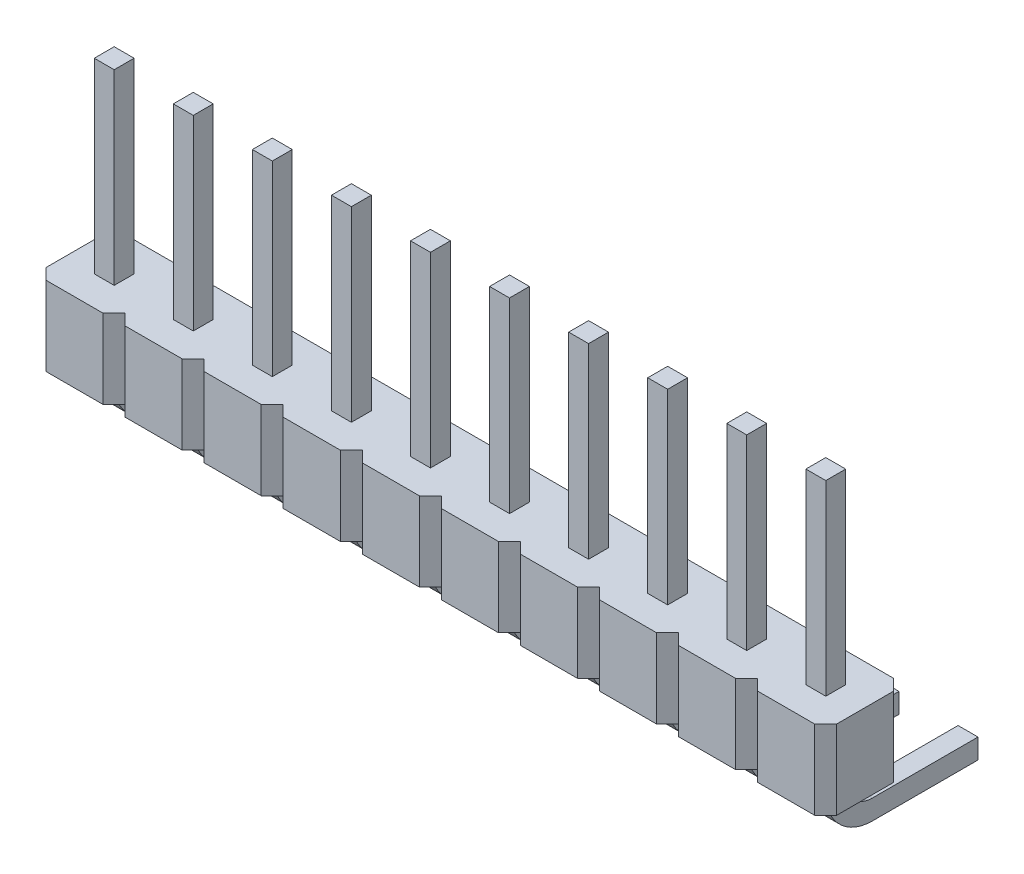
SolidWorks part; units mm, degrees
material "ABS"
ref_plane "Front Plane" through (0, 0, 0) normal (0, 0, 1) x (1, 0, 0)
ref_plane "Top Plane" through (0, 0, 0) normal (0, 1, 0) x (1, 0, 0)
ref_plane "Right Plane" through (0, 0, 0) normal (1, 0, 0) x (0, 0, -1)
sketch "Sketch1" plane through (0, 0, 0) normal (0, -1, 0) x (1, 0, 0)
  line L0 (-0.952, -1.2344) -> (-1.588, -1.2344)
  line L1 (-1.588, -1.2344) -> (-1.588, -0.5984)
  line L2 (-1.588, -0.5984) -> (-0.952, -0.5984)
  line L3 (-0.952, -0.5984) -> (-0.952, -1.2344)
  line L4 (-0.3536, -2.1864) -> (-2.1864, -2.1864)
  line L5 (-2.1864, 0.3536) -> (-2.1864, -2.1864) construction
  line L6 (-1.27, -0.5984) -> (-1.27, 0.3536) construction
  line L15 (-0.3536, -2.1864) -> (-2.1864, -2.1864) construction
  line L17 (-0.952, -0.9164) -> (0, -0.9164) construction
  line L54 (-0.3536, -2.1864) -> (0, -1.8329)
  line L56 (0, 0) -> (-0.3536, 0.3536)
  line L57 (-0.3536, 0.3536) -> (-2.1864, 0.3536)
  line L58 (-2.1864, 0.3536) -> (-2.54, 0)
  line L59 (-2.54, 0) -> (-2.54, -1.8329)
  line L60 (-2.54, -1.8329) -> (-2.1864, -2.1864)
  line L323 (0, 0) -> (0, -1.8329)
  line L563 (-0.952, -3.7744) -> (-1.588, -3.7744) [skipped]
  line L564 (-1.588, -3.7744) -> (-1.588, -3.1384) [skipped]
  line L565 (-1.588, -3.1384) -> (-0.952, -3.1384) [skipped]
  line L566 (-0.952, -3.1384) -> (-0.952, -3.7744) [skipped]
  line L567 (-2.1864, -2.1864) -> (-2.54, -2.54) [skipped]
  line L568 (-2.54, -2.54) -> (-2.54, -4.3729) [skipped]
  line L569 (-2.54, -4.3729) -> (-2.1864, -4.7264) [skipped]
  line L570 (-0.952, -6.3144) -> (-1.588, -6.3144) [skipped]
  line L571 (-1.588, -6.3144) -> (-1.588, -5.6784) [skipped]
  line L572 (-1.588, -5.6784) -> (-0.952, -5.6784) [skipped]
  line L573 (-0.952, -5.6784) -> (-0.952, -6.3144) [skipped]
  line L574 (-2.1864, -4.7264) -> (-2.54, -5.08) [skipped]
  line L575 (-2.54, -5.08) -> (-2.54, -6.9129) [skipped]
  line L576 (-2.54, -6.9129) -> (-2.1864, -7.2664) [skipped]
  line L577 (-0.952, -8.8544) -> (-1.588, -8.8544) [skipped]
  line L578 (-1.588, -8.8544) -> (-1.588, -8.2184) [skipped]
  line L579 (-1.588, -8.2184) -> (-0.952, -8.2184) [skipped]
  line L580 (-0.952, -8.2184) -> (-0.952, -8.8544) [skipped]
  line L581 (-2.1864, -7.2664) -> (-2.54, -7.62) [skipped]
  line L582 (-2.54, -7.62) -> (-2.54, -9.4529) [skipped]
  line L583 (-2.54, -9.4529) -> (-2.1864, -9.8064) [skipped]
  line L584 (-0.952, -11.3944) -> (-1.588, -11.3944) [skipped]
  line L585 (-1.588, -11.3944) -> (-1.588, -10.7584) [skipped]
  line L586 (-1.588, -10.7584) -> (-0.952, -10.7584) [skipped]
  line L587 (-0.952, -10.7584) -> (-0.952, -11.3944) [skipped]
  line L588 (-2.1864, -9.8064) -> (-2.54, -10.16) [skipped]
  line L589 (-2.54, -10.16) -> (-2.54, -11.9929) [skipped]
  line L590 (-2.54, -11.9929) -> (-2.1864, -12.3464) [skipped]
  line L591 (-0.952, -13.9344) -> (-1.588, -13.9344) [skipped]
  line L592 (-1.588, -13.9344) -> (-1.588, -13.2984) [skipped]
  line L593 (-1.588, -13.2984) -> (-0.952, -13.2984) [skipped]
  line L594 (-0.952, -13.2984) -> (-0.952, -13.9344) [skipped]
  line L595 (-2.1864, -12.3464) -> (-2.54, -12.7) [skipped]
  line L596 (-2.54, -12.7) -> (-2.54, -14.5329) [skipped]
  line L597 (-2.54, -14.5329) -> (-2.1864, -14.8864) [skipped]
  line L598 (-2.1864, -14.8864) -> (-2.54, -15.24) [skipped]
  line L615 (-0.3536, -4.7264) -> (-2.1864, -4.7264) construction
  line L616 (-0.3536, -4.7264) -> (0, -4.3729) construction
  line L618 (0, -2.54) -> (-0.3536, -2.1864) construction
  line L620 (-1.27, -3.1384) -> (-1.27, -2.1864) construction
  line L621 (-0.3536, -7.2664) -> (-2.1864, -7.2664) construction
  line L622 (-0.3536, -7.2664) -> (0, -6.9129) construction
  line L624 (0, -5.08) -> (-0.3536, -4.7264) construction
  line L625 (-0.3536, -4.7264) -> (-2.1864, -4.7264) construction
  line L627 (-1.27, -5.6784) -> (-1.27, -4.7264) construction
  line L628 (-0.3536, -9.8064) -> (-2.1864, -9.8064) construction
  line L629 (-0.3536, -9.8064) -> (0, -9.4529) construction
  line L631 (0, -7.62) -> (-0.3536, -7.2664) construction
  line L632 (-0.3536, -7.2664) -> (-2.1864, -7.2664) construction
  line L634 (-1.27, -8.2184) -> (-1.27, -7.2664) construction
  line L635 (-0.3536, -12.3464) -> (-2.1864, -12.3464) construction
  line L636 (-0.3536, -12.3464) -> (0, -11.9929) construction
  line L638 (0, -10.16) -> (-0.3536, -9.8064) construction
  line L639 (-0.3536, -9.8064) -> (-2.1864, -9.8064) construction
  line L641 (-1.27, -10.7584) -> (-1.27, -9.8064) construction
  line L642 (-0.3536, -14.8864) -> (-2.1864, -14.8864) construction
  line L643 (-0.3536, -14.8864) -> (0, -14.5329) construction
  line L645 (0, -12.7) -> (-0.3536, -12.3464) construction
  line L646 (-0.3536, -12.3464) -> (-2.1864, -12.3464) construction
  line L648 (-1.27, -13.2984) -> (-1.27, -12.3464) construction
  line L649 (0, -15.24) -> (-0.3536, -14.8864) construction
  line L650 (-0.3536, -14.8864) -> (-2.1864, -14.8864) construction
  line L651 (-1.27, -15.8384) -> (-1.27, -14.8864) construction
  line L652 (-0.952, -16.4744) -> (-1.588, -16.4744) [skipped]
  line L653 (-1.588, -16.4744) -> (-1.588, -15.8384) [skipped]
  line L654 (-1.588, -15.8384) -> (-0.952, -15.8384) [skipped]
  line L655 (-0.952, -15.8384) -> (-0.952, -16.4744) [skipped]
  line L656 (-2.54, -15.24) -> (-2.54, -17.0729) [skipped]
  line L657 (-2.54, -17.0729) -> (-2.1864, -17.4264) [skipped]
  line L658 (-0.952, -19.0144) -> (-1.588, -19.0144) [skipped]
  line L659 (-1.588, -19.0144) -> (-1.588, -18.3784) [skipped]
  line L660 (-1.588, -18.3784) -> (-0.952, -18.3784) [skipped]
  line L661 (-0.952, -18.3784) -> (-0.952, -19.0144) [skipped]
  line L662 (-2.1864, -17.4264) -> (-2.54, -17.78) [skipped]
  line L663 (-2.54, -17.78) -> (-2.54, -19.6129) [skipped]
  line L664 (-2.54, -19.6129) -> (-2.1864, -19.9664) [skipped]
  line L665 (-0.952, -21.5544) -> (-1.588, -21.5544) [skipped]
  line L666 (-1.588, -21.5544) -> (-1.588, -20.9184) [skipped]
  line L667 (-1.588, -20.9184) -> (-0.952, -20.9184) [skipped]
  line L668 (-0.952, -20.9184) -> (-0.952, -21.5544) [skipped]
  line L669 (-2.1864, -19.9664) -> (-2.54, -20.32) [skipped]
  line L670 (-2.54, -20.32) -> (-2.54, -22.1529) [skipped]
  line L671 (-2.54, -22.1529) -> (-2.1864, -22.5064) [skipped]
  line L672 (-0.952, -24.0944) -> (-1.588, -24.0944) [skipped]
  line L673 (-1.588, -24.0944) -> (-1.588, -23.4584) [skipped]
  line L674 (-1.588, -23.4584) -> (-0.952, -23.4584) [skipped]
  line L675 (-0.952, -23.4584) -> (-0.952, -24.0944) [skipped]
  line L676 (-2.1864, -22.5064) -> (-2.54, -22.86) [skipped]
  line L677 (-2.54, -22.86) -> (-2.54, -24.6929) [skipped]
  line L678 (-2.54, -24.6929) -> (-2.1864, -25.0464) [skipped]
  line L679 (-0.952, -26.6344) -> (-1.588, -26.6344) [skipped]
  line L680 (-1.588, -26.6344) -> (-1.588, -25.9984) [skipped]
  line L681 (-1.588, -25.9984) -> (-0.952, -25.9984) [skipped]
  line L682 (-0.952, -25.9984) -> (-0.952, -26.6344) [skipped]
  line L683 (-2.1864, -25.0464) -> (-2.54, -25.4) [skipped]
  line L684 (-2.54, -25.4) -> (-2.54, -27.2329) [skipped]
  line L685 (-2.54, -27.2329) -> (-2.1864, -27.5864) [skipped]
  line L686 (-0.952, -29.1744) -> (-1.588, -29.1744) [skipped]
  line L687 (-1.588, -29.1744) -> (-1.588, -28.5384) [skipped]
  line L688 (-1.588, -28.5384) -> (-0.952, -28.5384) [skipped]
  line L689 (-0.952, -28.5384) -> (-0.952, -29.1744) [skipped]
  line L690 (-2.1864, -27.5864) -> (-2.54, -27.94) [skipped]
  line L691 (-2.54, -27.94) -> (-2.54, -29.7729) [skipped]
  line L692 (-2.54, -29.7729) -> (-2.1864, -30.1264) [skipped]
  line L693 (-0.952, -31.7144) -> (-1.588, -31.7144) [skipped]
  line L694 (-1.588, -31.7144) -> (-1.588, -31.0784) [skipped]
  line L695 (-1.588, -31.0784) -> (-0.952, -31.0784) [skipped]
  line L696 (-0.952, -31.0784) -> (-0.952, -31.7144) [skipped]
  line L697 (-2.1864, -30.1264) -> (-2.54, -30.48) [skipped]
  line L698 (-2.54, -30.48) -> (-2.54, -32.3129) [skipped]
  line L699 (-2.54, -32.3129) -> (-2.1864, -32.6664) [skipped]
  line L700 (-0.952, -34.2544) -> (-1.588, -34.2544) [skipped]
  line L701 (-1.588, -34.2544) -> (-1.588, -33.6184) [skipped]
  line L702 (-1.588, -33.6184) -> (-0.952, -33.6184) [skipped]
  line L703 (-0.952, -33.6184) -> (-0.952, -34.2544) [skipped]
  line L704 (-2.1864, -32.6664) -> (-2.54, -33.02) [skipped]
  line L705 (-2.54, -33.02) -> (-2.54, -34.8529) [skipped]
  line L706 (-2.54, -34.8529) -> (-2.1864, -35.2064) [skipped]
  line L707 (-0.952, -36.7944) -> (-1.588, -36.7944) [skipped]
  line L708 (-1.588, -36.7944) -> (-1.588, -36.1584) [skipped]
  line L709 (-1.588, -36.1584) -> (-0.952, -36.1584) [skipped]
  line L710 (-0.952, -36.1584) -> (-0.952, -36.7944) [skipped]
  line L711 (-2.1864, -35.2064) -> (-2.54, -35.56) [skipped]
  line L712 (-2.54, -35.56) -> (-2.54, -37.3929) [skipped]
  line L713 (-2.54, -37.3929) -> (-2.1864, -37.7464) [skipped]
  line L714 (-0.952, -39.3344) -> (-1.588, -39.3344) [skipped]
  line L715 (-1.588, -39.3344) -> (-1.588, -38.6984) [skipped]
  line L716 (-1.588, -38.6984) -> (-0.952, -38.6984) [skipped]
  line L717 (-0.952, -38.6984) -> (-0.952, -39.3344) [skipped]
  line L718 (-2.1864, -37.7464) -> (-2.54, -38.1) [skipped]
  line L719 (-2.54, -38.1) -> (-2.54, -39.9329) [skipped]
  line L720 (-2.54, -39.9329) -> (-2.1864, -40.2864) [skipped]
  line L721 (-0.952, -41.8744) -> (-1.588, -41.8744) [skipped]
  line L722 (-1.588, -41.8744) -> (-1.588, -41.2384) [skipped]
  line L723 (-1.588, -41.2384) -> (-0.952, -41.2384) [skipped]
  line L724 (-0.952, -41.2384) -> (-0.952, -41.8744) [skipped]
  line L725 (-2.1864, -40.2864) -> (-2.54, -40.64) [skipped]
  line L726 (-2.54, -40.64) -> (-2.54, -42.4729) [skipped]
  line L727 (-2.54, -42.4729) -> (-2.1864, -42.8264) [skipped]
  line L728 (-0.952, -44.4144) -> (-1.588, -44.4144) [skipped]
  line L729 (-1.588, -44.4144) -> (-1.588, -43.7784) [skipped]
  line L730 (-1.588, -43.7784) -> (-0.952, -43.7784) [skipped]
  line L731 (-0.952, -43.7784) -> (-0.952, -44.4144) [skipped]
  line L732 (-2.1864, -42.8264) -> (-2.54, -43.18) [skipped]
  line L733 (-2.54, -43.18) -> (-2.54, -45.0129) [skipped]
  line L734 (-2.54, -45.0129) -> (-2.1864, -45.3664) [skipped]
  line L735 (-0.952, -46.9544) -> (-1.588, -46.9544) [skipped]
  line L736 (-1.588, -46.9544) -> (-1.588, -46.3184) [skipped]
  line L737 (-1.588, -46.3184) -> (-0.952, -46.3184) [skipped]
  line L738 (-0.952, -46.3184) -> (-0.952, -46.9544) [skipped]
  line L739 (-2.1864, -45.3664) -> (-2.54, -45.72) [skipped]
  line L740 (-2.54, -45.72) -> (-2.54, -47.5529) [skipped]
  line L741 (-2.54, -47.5529) -> (-2.1864, -47.9064) [skipped]
  line L742 (-0.952, -49.4944) -> (-1.588, -49.4944) [skipped]
  line L743 (-1.588, -49.4944) -> (-1.588, -48.8584) [skipped]
  line L744 (-1.588, -48.8584) -> (-0.952, -48.8584) [skipped]
  line L745 (-0.952, -48.8584) -> (-0.952, -49.4944) [skipped]
  line L746 (-2.1864, -47.9064) -> (-2.54, -48.26) [skipped]
  line L747 (-2.54, -48.26) -> (-2.54, -50.0929) [skipped]
  line L748 (-2.54, -50.0929) -> (-2.1864, -50.4464) [skipped]
  line L790 (-0.3536, -17.4264) -> (-2.1864, -17.4264) construction
  line L791 (-0.3536, -17.4264) -> (0, -17.0729) construction
  line L794 (-0.3536, -19.9664) -> (-2.1864, -19.9664) construction
  line L795 (-0.3536, -19.9664) -> (0, -19.6129) construction
  line L797 (0, -17.78) -> (-0.3536, -17.4264) construction
  line L798 (-0.3536, -17.4264) -> (-2.1864, -17.4264) construction
  line L800 (-1.27, -18.3784) -> (-1.27, -17.4264) construction
  line L801 (-0.3536, -22.5064) -> (-2.1864, -22.5064) construction
  line L802 (-0.3536, -22.5064) -> (0, -22.1529) construction
  line L804 (0, -20.32) -> (-0.3536, -19.9664) construction
  line L805 (-0.3536, -19.9664) -> (-2.1864, -19.9664) construction
  line L807 (-1.27, -20.9184) -> (-1.27, -19.9664) construction
  line L808 (-0.3536, -25.0464) -> (-2.1864, -25.0464) construction
  line L809 (-0.3536, -25.0464) -> (0, -24.6929) construction
  line L811 (0, -22.86) -> (-0.3536, -22.5064) construction
  line L812 (-0.3536, -22.5064) -> (-2.1864, -22.5064) construction
  line L814 (-1.27, -23.4584) -> (-1.27, -22.5064) construction
  line L815 (-0.3536, -27.5864) -> (-2.1864, -27.5864) construction
  line L816 (-0.3536, -27.5864) -> (0, -27.2329) construction
  line L818 (0, -25.4) -> (-0.3536, -25.0464) construction
  line L819 (-0.3536, -25.0464) -> (-2.1864, -25.0464) construction
  line L821 (-1.27, -25.9984) -> (-1.27, -25.0464) construction
  line L822 (-0.3536, -30.1264) -> (-2.1864, -30.1264) construction
  line L823 (-0.3536, -30.1264) -> (0, -29.7729) construction
  line L825 (0, -27.94) -> (-0.3536, -27.5864) construction
  line L826 (-0.3536, -27.5864) -> (-2.1864, -27.5864) construction
  line L828 (-1.27, -28.5384) -> (-1.27, -27.5864) construction
  line L829 (-0.3536, -32.6664) -> (-2.1864, -32.6664) construction
  line L830 (-0.3536, -32.6664) -> (0, -32.3129) construction
  line L832 (0, -30.48) -> (-0.3536, -30.1264) construction
  line L833 (-0.3536, -30.1264) -> (-2.1864, -30.1264) construction
  line L835 (-1.27, -31.0784) -> (-1.27, -30.1264) construction
  line L836 (-0.3536, -35.2064) -> (-2.1864, -35.2064) construction
  line L837 (-0.3536, -35.2064) -> (0, -34.8529) construction
  line L839 (0, -33.02) -> (-0.3536, -32.6664) construction
  line L840 (-0.3536, -32.6664) -> (-2.1864, -32.6664) construction
  line L842 (-1.27, -33.6184) -> (-1.27, -32.6664) construction
  line L843 (-0.3536, -37.7464) -> (-2.1864, -37.7464) construction
  line L844 (-0.3536, -37.7464) -> (0, -37.3929) construction
  line L846 (0, -35.56) -> (-0.3536, -35.2064) construction
  line L847 (-0.3536, -35.2064) -> (-2.1864, -35.2064) construction
  line L849 (-1.27, -36.1584) -> (-1.27, -35.2064) construction
  line L850 (-0.3536, -40.2864) -> (-2.1864, -40.2864) construction
  line L851 (-0.3536, -40.2864) -> (0, -39.9329) construction
  line L853 (0, -38.1) -> (-0.3536, -37.7464) construction
  line L854 (-0.3536, -37.7464) -> (-2.1864, -37.7464) construction
  line L856 (-1.27, -38.6984) -> (-1.27, -37.7464) construction
  line L857 (-0.3536, -42.8264) -> (-2.1864, -42.8264) construction
  line L858 (-0.3536, -42.8264) -> (0, -42.4729) construction
  line L860 (0, -40.64) -> (-0.3536, -40.2864) construction
  line L861 (-0.3536, -40.2864) -> (-2.1864, -40.2864) construction
  line L863 (-1.27, -41.2384) -> (-1.27, -40.2864) construction
  line L864 (-0.3536, -45.3664) -> (-2.1864, -45.3664) construction
  line L865 (-0.3536, -45.3664) -> (0, -45.0129) construction
  line L867 (0, -43.18) -> (-0.3536, -42.8264) construction
  line L868 (-0.3536, -42.8264) -> (-2.1864, -42.8264) construction
  line L870 (-1.27, -43.7784) -> (-1.27, -42.8264) construction
  line L871 (-0.3536, -47.9064) -> (-2.1864, -47.9064) construction
  line L872 (-0.3536, -47.9064) -> (0, -47.5529) construction
  line L874 (0, -45.72) -> (-0.3536, -45.3664) construction
  line L875 (-0.3536, -45.3664) -> (-2.1864, -45.3664) construction
  line L877 (-1.27, -46.3184) -> (-1.27, -45.3664) construction
  line L878 (-0.3536, -50.4464) -> (-2.1864, -50.4464) construction
  line L879 (-0.3536, -50.4464) -> (0, -50.0929) construction
  line L881 (0, -48.26) -> (-0.3536, -47.9064) construction
  line L882 (-0.3536, -47.9064) -> (-2.1864, -47.9064) construction
  line L884 (-1.27, -48.8584) -> (-1.27, -47.9064) construction
  line L885 (2.1864, 0.3536) -> (0.3536, 0.3536) construction
  line L886 (1.588, -1.2344) -> (0.952, -1.2344) [skipped]
  line L887 (0.952, -1.2344) -> (0.952, -0.5984) [skipped]
  line L888 (0.952, -0.5984) -> (1.588, -0.5984) [skipped]
  line L889 (1.588, -0.5984) -> (1.588, -1.2344) [skipped]
  line L890 (2.1864, -2.1864) -> (16.4995, 12.1266) [skipped]
  line L891 (-9.9832, 12.5232) -> (2.1864, 0.3536) [skipped]
  line L892 (2.1864, -2.1864) -> (0.3536, -2.1864) construction
  line L894 (1.27, -0.5984) -> (1.27, 0.3536) construction
  line L895 (2.1864, -2.1864) -> (0.3536, -2.1864) construction
  line L897 (0, -1.8329) -> (0.3536, -2.1864) construction
  line L898 (0.3536, 0.3536) -> (0, 0) construction
  dimension "D1" = 0.636
  dimension "D7" = 0.5
  dimension "D3" = 45
  dimension "D4" = 2.54
  dimension "D6" = 2.54
  dimension "D2" = 20
  dimension "D8" = 2
extrude "Boss-Extrude1" add sketch "Sketch1" against normal blind 2.54
sketch "Esquisse1" plane through (-1.588, 0, 0) normal (1, 0, 0) x (0, 0, -1)
  line L0 (0.5984, 8.54) -> (0.5984, -0.18)
  line L1 (1.2384, -0.18) -> (1.2384, 8.54)
  line L2 (1.2384, 8.54) -> (0.5984, 8.54)
  line L3 (2.0984, -1.04) -> (5.4884, -1.04)
  line L4 (5.4884, -1.04) -> (5.4884, -1.68)
  line L5 (5.4884, -1.68) -> (2.0984, -1.68)
  arc A0 (0.5984, -0.18) -> (2.0984, -1.68) centre (2.0984, -0.18) ccw
  arc A1 (2.0984, -1.04) -> (1.2384, -0.18) centre (2.0984, -0.18) cw
  point P0 (0.5984, 2.54)
  point P6 (0.5984, 2.54)
  point P11 (0.5984, 2.54)
  point P13 (0.5984, 5.363)
  point P14 (0.5984, 4.5366)
  point P15 (2.0984, -2.7171)
  dimension "D2" = 1.5
  dimension "D1" = 0.64
  dimension "D3" = 4.89
  dimension "D4" = 10.22
  dimension "D5" = 6
extrude "Boss.-Extru.1" add sketch "Esquisse1" along normal blind 0.64
pattern_linear "Répétition linéaire1" count 10 spacing 2.54 along (1, 0, 0) of "Boss.-Extru.1", "Boss-Extrude1"
equation "\"D1@Boss-Extrude1\"= \"D4@Sketch1\""
equation "\"D6@Sketch1\"=\"D4@Sketch1\""
